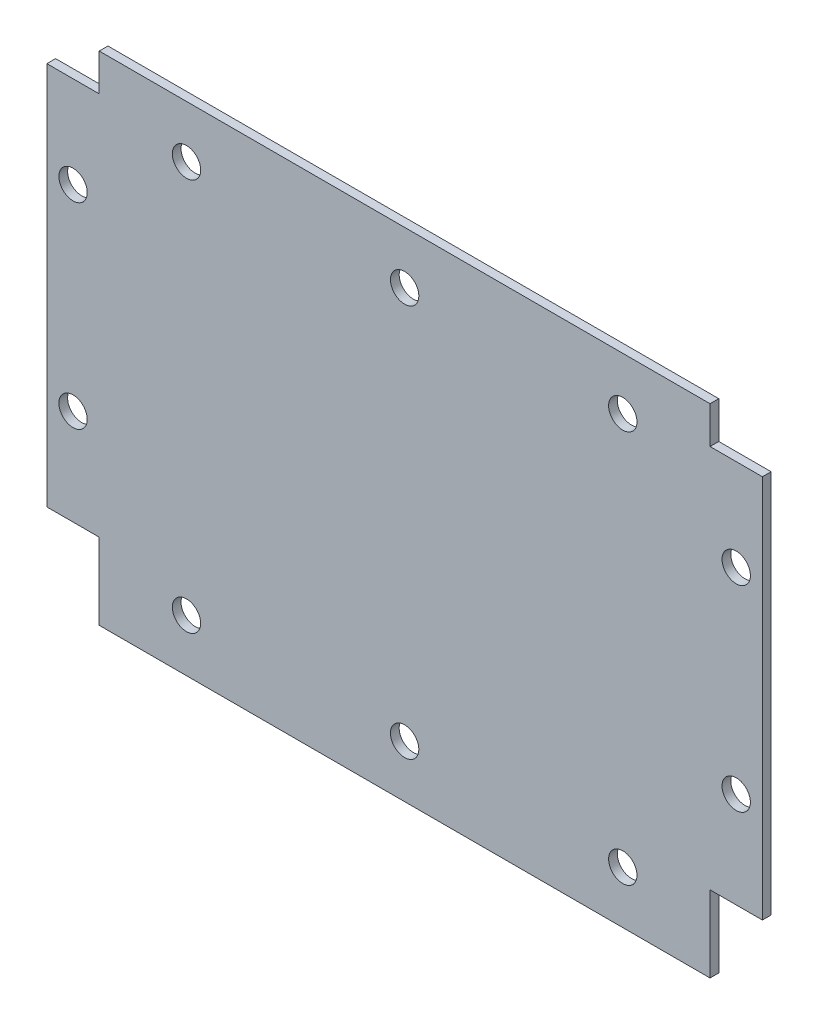
SolidWorks part; units mm, degrees
material "Ст 3 ГОСТ 380-2005"
ref_plane "Спереди" through (0, 0, 0) normal (0, 0, 1) x (1, 0, 0)
ref_plane "Сверху" through (0, 0, 0) normal (0, 1, 0) x (1, 0, 0)
ref_plane "Слева" through (0, 0, 0) normal (1, 0, 0) x (0, 0, -1)
sketch "Эскиз1" plane through (0, 0, 0) normal (0, 0, 1) x (1, 0, 0)
  line L0 (-70, 48.5) -> (-70, 57)
  line L1 (-70, -57) -> (70, -57)
  line L2 (-70, -57) -> (-70, -39.5)
  line L3 (-70, 57) -> (70, 57)
  line L4 (70, -57) -> (70, -39.5)
  line L5 (-70, -57) -> (70, 57) construction
  line L6 (-70, 57) -> (70, -57) construction
  line L7 (-82, 48.5) -> (-70, 48.5)
  line L8 (-82, 48.5) -> (-82, -39.5)
  line L9 (-82, -39.5) -> (-70, -39.5)
  line L10 (82, 48.5) -> (82, -39.5)
  line L11 (70, -39.5) -> (82, -39.5)
  line L12 (70, 48.5) -> (70, 57)
  line L13 (70, 48.5) -> (82, 48.5)
  line L14 (0, 0) -> (0, -39.7711) construction
  point P0 (0, 0)
  dimension "D1" = 140
  dimension "D2" = 164
  dimension "D3" = 17.5
  dimension "D4" = 88
  dimension "D5" = 114
extrude "Вытянуть1" add sketch "Эскиз1" along normal blind 2
sketch "Эскиз2" plane through (0, 0, 2) normal (0, 0, 1) x (1, 0, 0)
  line L0 (0, 0) -> (0, 27.5) construction
  line L1 (-50, -45) -> (50, -45)
  line L2 (-50, -45) -> (-50, 45)
  line L3 (-50, 45) -> (50, 45)
  line L4 (50, -45) -> (50, 45)
  line L5 (-50, -45) -> (50, 45) construction
  line L6 (-50, 45) -> (50, -45) construction
  line L7 (-76, 27.5) -> (76, 27.5)
  line L8 (-76, 27.5) -> (-76, -17.5)
  line L9 (-76, -17.5) -> (76, -17.5)
  line L10 (76, 27.5) -> (76, -17.5)
  line L11 (-70, -57) -> (70, -57) construction
  point P0 (0, 0)
  dimension "D1" = 100
  dimension "D2" = 12
  dimension "D3" = 90
  dimension "D4" = 152
  dimension "D5" = 27.5
  dimension "D6" = 45
hole_wizard "Отверстие с зазором M61" positions "Трехмерный эскиз1" profile "Эскиз3" hole size "M6" standard "ГОСТ" end condition through all
sketch3d "Трехмерный эскиз1"
  line L0 (-50, 45, 2) -> (50, 45, 2) construction
  line L1 (-50, -45, 2) -> (50, -45, 2) construction
  point P0 (-76, 27.5, 2)
  point P3 (-76, -17.5, 2)
  point P6 (-50, -45, 2)
  point P9 (0, -45, 2)
  point P11 (50, -45, 2)
  point P14 (50, 45, 2)
  point P17 (0, 45, 2)
  point P19 (-50, 45, 2)
  point P22 (76, 27.5, 2)
  point P25 (76, -17.5, 2)
sketch "Эскиз3" plane through (-76, 27.5, 2) normal (1, 0, 0) x (0, -1, 0)
  line L0 (0, 0) -> (0, 2)
  line L1 (0, 2) -> (3.25, 2)
  line L2 (3.25, 2) -> (3.25, 0)
  line L5 (3.25, 0) -> (0, 0)
  line L11 (0, -6.35) -> (0, 107.95) construction
  dimension "Диаметр сквозного отверстия" = 6.5
  dimension "Глубина сквозного отверстия" = 2
